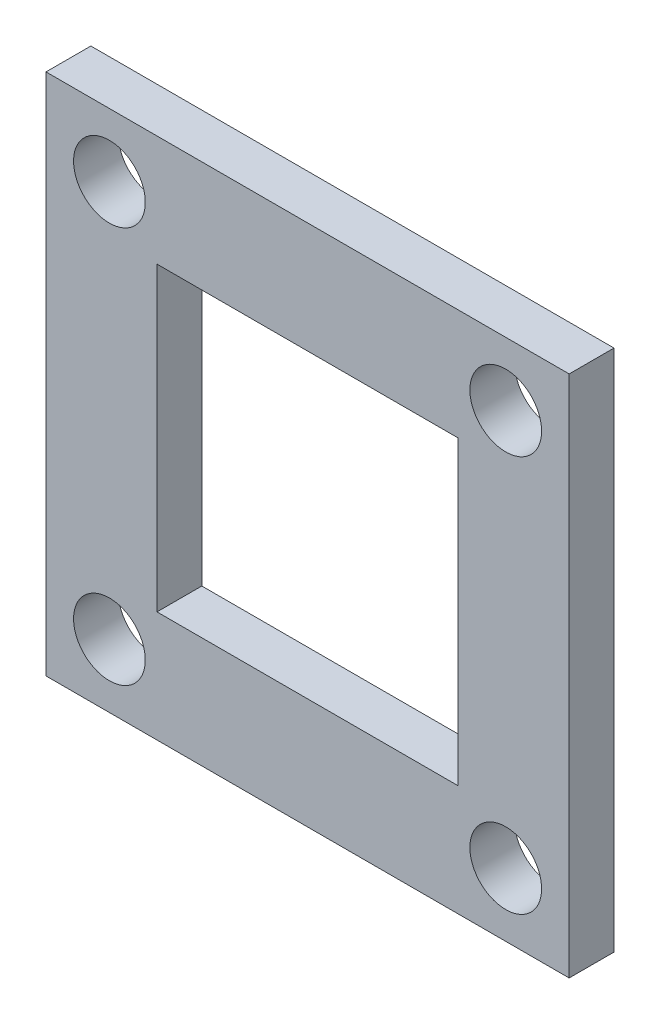
SolidWorks part; units mm, degrees
ref_plane "Plan de face" through (0, 0, 0) normal (0, 0, 1) x (1, 0, 0)
ref_plane "Plan de dessus" through (0, 0, 0) normal (0, 1, 0) x (1, 0, 0)
ref_plane "Plan de droite" through (0, 0, 0) normal (1, 0, 0) x (0, 0, -1)
sketch "Sketch1" plane through (0, 0, 0) normal (0, 0, 1) x (1, 0, 0)
  line L1 (-11.6673, -11.6673) -> (11.6673, -11.6673)
  line L2 (-11.6673, -11.6673) -> (-11.6673, 11.6673)
  line L3 (-11.6673, 11.6673) -> (11.6673, 11.6673)
  line L4 (11.6673, -11.6673) -> (11.6673, 11.6673)
  line L5 (-11.6673, -11.6673) -> (11.6673, 11.6673) construction
  line L6 (-11.6673, 11.6673) -> (11.6673, -11.6673) construction
  line L7 (-6.7175, -6.7175) -> (6.7175, -6.7175)
  line L8 (-6.7175, -6.7175) -> (-6.7175, 6.7175)
  line L9 (-6.7175, 6.7175) -> (6.7175, 6.7175)
  line L10 (6.7175, -6.7175) -> (6.7175, 6.7175)
  line L11 (-6.7175, -6.7175) -> (6.7175, 6.7175) construction
  line L12 (-6.7175, 6.7175) -> (6.7175, -6.7175) construction
  point P0 (0, 0)
  point P6 (0, 0)
  dimension "D1" = 16.5
  dimension "D2" = 9.5
extrude "Boss-Extrude1" add sketch "Sketch1" along normal mid plane 2
sketch "Sketch2" plane through (0, 0, -1) normal (0, 0, -1) x (-1, 0, 0)
  circle A1 centre (8.8388, -8.8388) radius 1.6
  circle A2 centre (8.8388, -8.8388) radius 1.6
  circle A3 centre (8.8388, 8.8388) radius 1.6
  circle A4 centre (8.8388, 8.8388) radius 1.6
  circle A5 centre (-8.8388, -8.8388) radius 1.6
  circle A6 centre (-8.8388, -8.8388) radius 1.6
  circle A7 centre (-8.8388, 8.8388) radius 1.6
  circle A8 centre (-8.8388, 8.8388) radius 1.6
  dimension "D1" = 0
  dimension "D2" = 0
  dimension "D3" = 0
  dimension "D4" = 0
extrude "Cut-Extrude1" cut sketch "Sketch2" against normal through all
